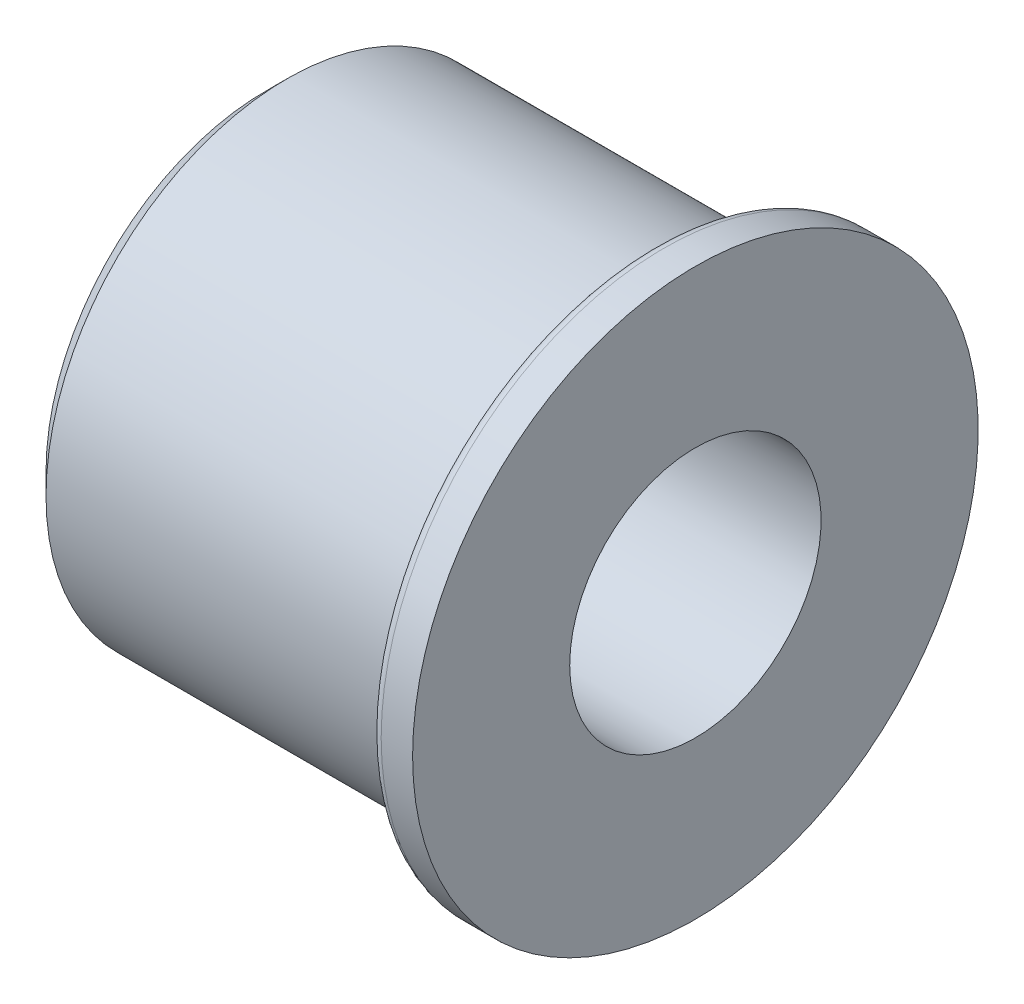
SolidWorks part; units mm, degrees
ref_plane "Plan de face" through (0, 0, 0) normal (0, 0, 1) x (1, 0, 0)
ref_plane "Plan de dessus" through (0, 0, 0) normal (0, 1, 0) x (1, 0, 0)
ref_plane "Plan de droite" through (0, 0, 0) normal (1, 0, 0) x (0, 0, -1)
sketch "Esquisse1" plane through (0, 0, 0) normal (0, 0, 1) x (1, 0, 0)
  line L0 (0, 0) -> (20.7387, 0) construction
  line L3 (0, 6) -> (20.5, 6)
  line L4 (0, 6) -> (0, 10.5)
  line L5 (20.5, 6) -> (20.5, 13.5)
  line L6 (20.5, 13.5) -> (19, 13.5)
  line L7 (18.5, 13) -> (18.5, 11.5)
  line L8 (1, 11.5) -> (18.5, 11.5)
  line L9 (0, 10.5) -> (1, 11.5)
  arc A0 (19, 13.5) -> (18.5, 13) centre (19, 13) ccw
  point P3 (0, 11.5)
  dimension "D1" = 0.5
  dimension "D2" = 6
  dimension "D3" = 11.5
  dimension "D5" = 20.5
  dimension "D6" = 18.5
  dimension "D7" = 2
revolve "Révolution1" add sketch "Esquisse1" angle 360 about L0
